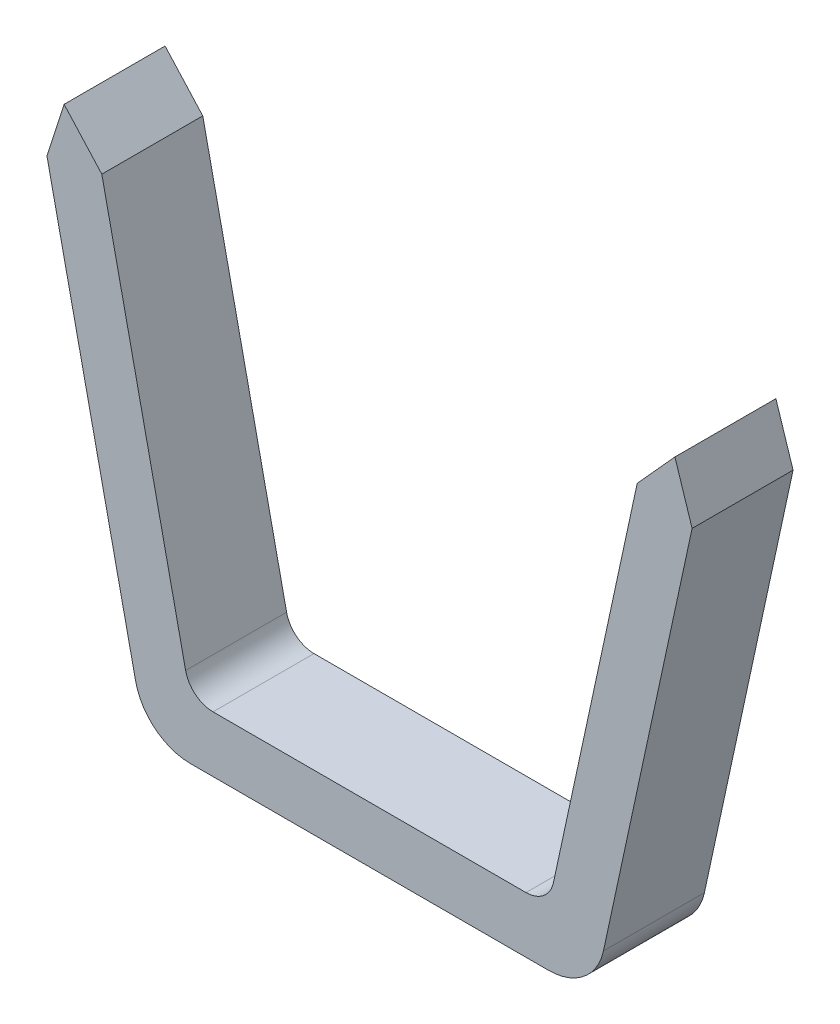
SolidWorks part; units mm, degrees
ref_plane "Front Plane" through (0, 0, 0) normal (0, 0, 1) x (1, 0, 0)
ref_plane "Top Plane" through (0, 0, 0) normal (0, 1, 0) x (1, 0, 0)
ref_plane "Right Plane" through (0, 0, 0) normal (1, 0, 0) x (0, 0, -1)
sketch "Sketch3" plane through (0, 0, 0) normal (0, 0, 1) x (1, 0, 0)
  line L0 (-31.9299, -122.5) -> (31.9299, -122.5)
  line L1 (41.7043, -114.6119) -> (73.3084, 31.6608)
  line L2 (-73.3084, 31.6608) -> (-41.7043, -114.6119)
  line L3 (-31.9299, -112.5) -> (-51.2845, -22.9211)
  line L4 (31.9299, -112.5) -> (51.2845, -22.9211)
  line L5 (-31.9299, -112.5) -> (31.9299, -112.5)
  line L6 (-55.4723, -3.5388) -> (-63.5339, 33.7727)
  line L8 (55.4723, -3.5388) -> (63.5339, 33.7727)
  arc A0 (31.9299, -122.5) -> (41.7043, -114.6119) centre (31.9299, -112.5) ccw
  arc A1 (73.3084, 31.6608) -> (-73.3084, 31.6608) centre (0, 47.5) ccw
  arc A2 (-41.7043, -114.6119) -> (-31.9299, -122.5) centre (-31.9299, -112.5) ccw
  circle A3 centre (50, -12.5) radius 4.5
  circle A4 centre (50, 87.5) radius 4.5
  circle A5 centre (-50, 87.5) radius 4.5
  circle A6 centre (-50, -12.5) radius 4.5
  arc A7 (63.5339, 33.7727) -> (56.6488, 79.3733) centre (0, 47.5) ccw
  arc A8 (-56.6488, 79.3733) -> (-43.531, 95.7706) centre (-50, 87.5) ccw
  arc A9 (43.531, 95.7706) -> (56.6488, 79.3733) centre (50, 87.5) ccw
  arc A10 (55.4723, -3.5388) -> (51.2845, -22.9211) centre (50, -12.5) ccw
  arc A11 (-51.2845, -22.9211) -> (-55.4723, -3.5388) centre (-50, -12.5) ccw
  arc A13 (43.531, 95.7706) -> (-43.531, 95.7706) centre (0, 47.5) ccw
  arc A15 (-56.6488, 79.3733) -> (-63.5339, 33.7727) centre (0, 47.5) ccw
  dimension "D1" = 10
  dimension "D2" = 6
  dimension "D3" = 10
  dimension "D4" = 10
  dimension "D5" = 10
  dimension "D6" = 6
  dimension "D7" = 6
  dimension "D8" = 6
extrude "Boss-Extrude1" add sketch "Sketch3" along normal blind 18
fillet "Fillet1" radius 5 2 edges at (31.9299, -112.5, 9) (-31.9299, -112.5, 9)
fillet "Fillet2" radius 5 8 edges at (-55.4723, -3.5388, 9) (55.4723, -3.5388, 9) (51.2845, -22.9211, 9) (-51.2845, -22.9211, 9) (56.6488, 79.3733, 9) (43.531, 95.7706, 9) (-43.531, 95.7706, 9) (-56.6488, 79.3733, 9)
sketch "Sketch5" plane through (0, 0, 18) normal (0, 0, 1) x (1, 0, 0)
  line L0 (0, 122.5) -> (106.1425, 122.5) construction
  line L1 (0, -122.5) -> (100.4685, -122.5) construction
  line L2 (-31.9299, -122.5) -> (31.9299, -122.5) construction
  line L3 (-47.7237, -39.4017) -> (0.048, -29.2744) construction
  line L4 (47.7244, -39.3984) -> (54.4443, -31.972)
  line L5 (-73.3084, 31.6608) -> (-41.7043, -114.6119) construction
  line L6 (0.048, -29.2744) -> (47.7244, -39.3984) construction
  line L7 (41.7043, -114.6119) -> (73.3084, 31.6608) construction
  line L8 (-57.5064, -41.4755) -> (-54.444, -31.9737)
  line L9 (-54.444, -31.9737) -> (-47.7237, -39.4017)
  line L10 (-50.1213, -28.305) -> (-32.782, -108.5559) construction
  line L11 (-47.7237, -39.4017) -> (47.7244, -39.3984)
  line L12 (32.782, -108.5559) -> (50.1213, -28.305) construction
  line L13 (54.4443, -31.972) -> (57.5064, -41.4755)
  line L14 (-57.5064, -41.4755) -> (-148.3367, 157.1304)
  line L15 (-148.3367, 157.1304) -> (172.5844, 157.1304)
  line L16 (172.5844, 157.1304) -> (57.5064, -41.4755)
  arc A0 (73.3084, 31.6608) -> (-73.3084, 31.6608) centre (0, 47.5) ccw construction
  dimension "D1" = 60
  dimension "D2" = 5
  dimension "D3" = 5
  dimension "D4" = 60
extrude "Cut-Extrude2" cut sketch "Sketch5" against normal through all
